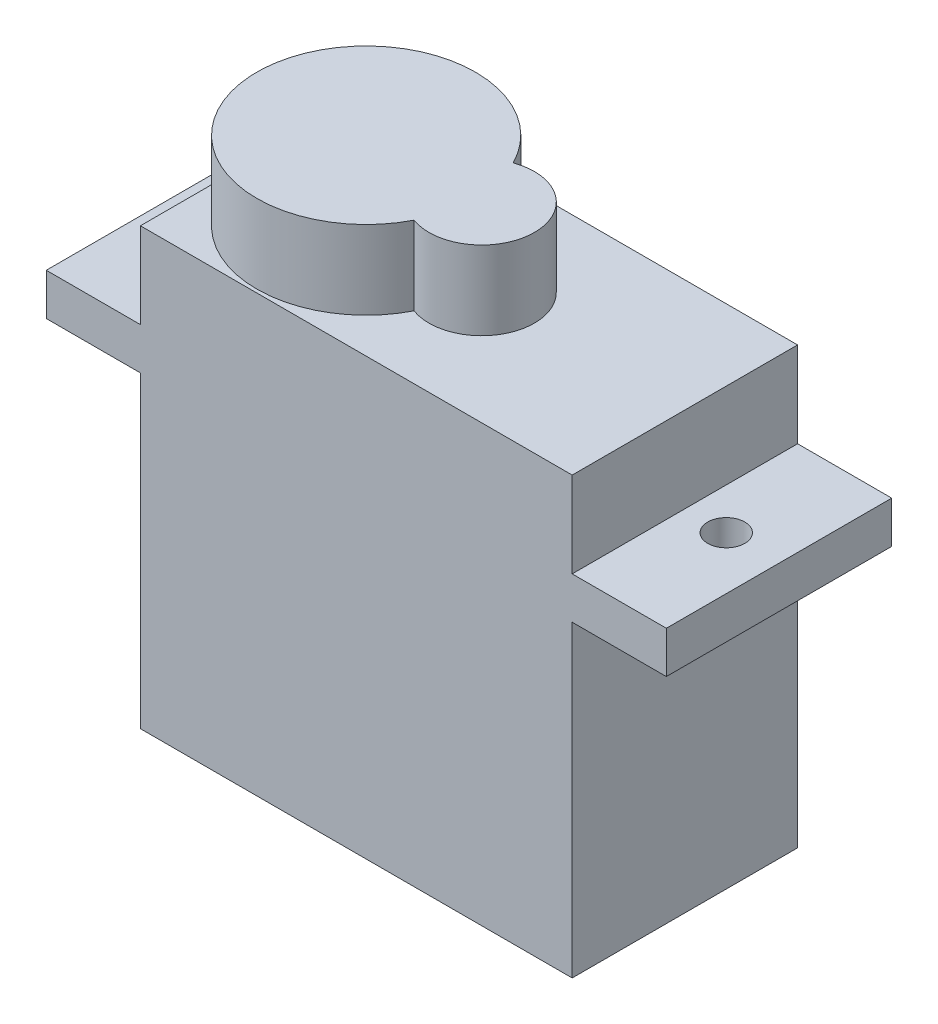
SolidWorks part; units mm, degrees
ref_plane "Front Plane" through (0, 0, 0) normal (0, 0, 1) x (1, 0, 0)
ref_plane "Top Plane" through (0, 0, 0) normal (0, 1, 0) x (1, 0, 0)
ref_plane "Right Plane" through (0, 0, 0) normal (1, 0, 0) x (0, 0, -1)
sketch "Sketch2" plane through (0, 0, 0) normal (0, 1, 0) x (1, 0, 0)
  line L1 (-16.3, -5.925) -> (16.3, -5.925)
  line L2 (-16.3, -5.925) -> (-16.3, 5.925)
  line L3 (-16.3, 5.925) -> (16.3, 5.925)
  line L4 (16.3, -5.925) -> (16.3, 5.925)
  line L5 (-16.3, -5.925) -> (16.3, 5.925) construction
  line L6 (-16.3, 5.925) -> (16.3, -5.925) construction
  point P0 (0, 0)
  dimension "D1" = 32.6
  dimension "D2" = 11.85
extrude "Boss-Extrude2" add sketch "Sketch2" along normal blind 2.2
sketch "Sketch3" plane through (0, 2.2, 0) normal (0, 1, 0) x (1, 0, 0)
  line L0 (16.3, 5.925) -> (-16.3, 5.925) construction
  line L1 (-11.35, -5.925) -> (11.35, -5.925)
  line L2 (-11.35, -5.925) -> (-11.35, 5.925)
  line L3 (-11.35, 5.925) -> (11.35, 5.925)
  line L4 (11.35, -5.925) -> (11.35, 5.925)
  line L5 (-11.35, -5.925) -> (11.35, 5.925) construction
  line L6 (-11.35, 5.925) -> (11.35, -5.925) construction
  point P0 (0, 0)
  dimension "D1" = 22.7
extrude "Boss-Extrude3" add sketch "Sketch3" along normal blind 4.5 and the other way blind 18.4
sketch "Sketch4" plane through (0, 2.2, 0) normal (0, 1, 0) x (1, 0, 0)
  line L0 (16.3, -5.925) -> (16.3, 5.925) construction
  circle A0 centre (13.525, 0) radius 0.975
  point P2 (16.3, 0)
  dimension "D2" = 1.95
  dimension "D1" = 2.775
extrude "Cut-Extrude1" cut sketch "Sketch4" against normal blind 4.5
mirror "Mirror1" about plane through (0, 0, 0) normal (1, 0, 0) of "Cut-Extrude1"
sketch "Sketch5" plane through (0, 6.7, 0) normal (0, 1, 0) x (1, 0, 0)
  circle A0 centre (-5.4081, 0) radius 5.75
  circle A1 centre (0.6669, 0) radius 2.775
  dimension "D1" = 11.5
  dimension "D2" = 5.55
  dimension "D3" = 6.075
extrude "Boss-Extrude4" add sketch "Sketch5" along normal blind 4.13 contours A0 | A1
